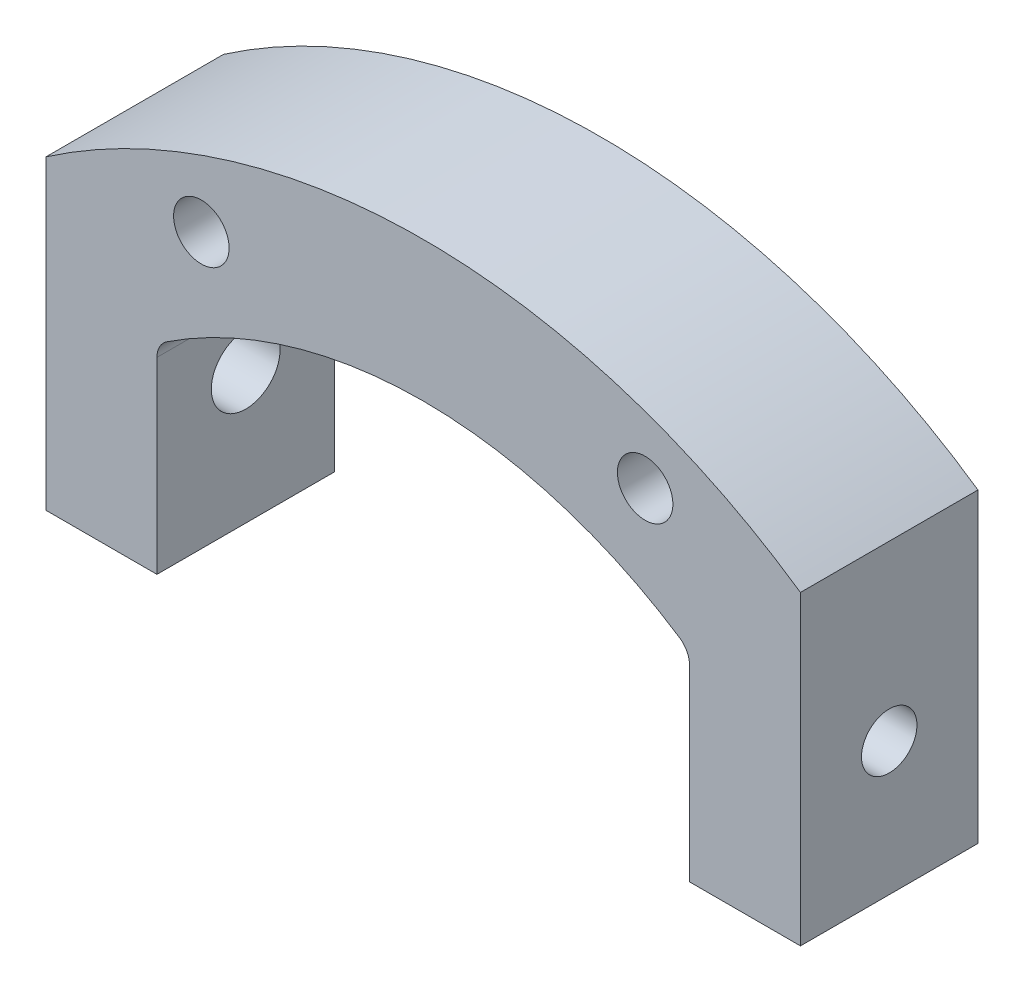
SolidWorks part; units mm, degrees
material "6061 合金"
ref_plane "前视基准面" through (0, 0, 0) normal (0, 0, 1) x (1, 0, 0)
ref_plane "上视基准面" through (0, 0, 0) normal (0, 1, 0) x (1, 0, 0)
ref_plane "右视基准面" through (0, 0, 0) normal (1, 0, 0) x (0, 0, -1)
sketch "草图4" plane through (0, 0, 0) normal (0, 0, 1) x (1, 0, 0)
  line L1 (-21.5, 5) -> (21.5, 5) construction
  line L2 (-21.5, 5) -> (-21.5, -5)
  line L3 (-21.5, -5) -> (21.5, -5)
  line L4 (21.5, 5) -> (21.5, -5)
  line L5 (0, -5) -> (0, 5) construction
  line L6 (-21.5, 0) -> (21.5, 0) construction
  arc A2 (-21.5, 5) -> (21.5, 5) centre (0, -15.9225) cw
  circle A3 centre (0, -18.9225) radius 30 construction
  circle A4 centre (-10, 9.3618) radius 1.25
  circle A5 centre (10, 9.3618) radius 1.25
  point P0 (0, 0)
  dimension "D3" = 20
  dimension "D6" = 30
  dimension "D7" = 60
  dimension "D9" = 2.5
  dimension "D1" = 43
  dimension "D2" = 10
  dimension "D8" = 3
extrude "凸台-拉伸2" add sketch "草图4" along normal blind 8
cosmetic thread "装饰螺纹线2" parameters "D2"=3
cosmetic thread "装饰螺纹线3" parameters "D2"=3
sketch "草图5" plane through (0, 0, 8) normal (0, 0, 1) x (1, 0, 0)
  line L0 (-21.5, -5) -> (21.5, -5) construction
  line L1 (-12, 4) -> (12, 4) construction
  line L2 (-12, 4) -> (-12, -5)
  line L3 (-12, -5) -> (12, -5)
  line L4 (12, 4) -> (12, -5)
  line L5 (0, -5) -> (0, 4) construction
  line L6 (-12, -0.5) -> (12, -0.5) construction
  line L7 (21.5, 13.1217) -> (17, 13.1217)
  line L8 (-21.5, -5) -> (-17, -5)
  line L9 (-21.5, -5) -> (-21.5, 13.1217)
  line L10 (-21.5, 13.1217) -> (-17, 13.1217)
  line L11 (-17, -5) -> (-17, 13.1217)
  line L12 (17, -5) -> (17, 13.1217)
  line L13 (21.5, -5) -> (17, -5)
  line L14 (21.5, -5) -> (21.5, 13.1217)
  arc A0 (-12, 4) -> (12, 4) centre (0, -13.2337) cw
  point P0 (0, -0.5)
  dimension "D3" = 21
  dimension "D1" = 9
  dimension "D2" = 24
  dimension "D4" = 5
extrude "切除-拉伸2" cut sketch "草图5" against normal through all
sketch "草图6" plane through (-17, 0, 0) normal (-1, 0, 0) x (0, 0, 1)
  line L0 (4, -5) -> (4, 8.7959) construction
  line L1 (0, -5) -> (8, -5) construction
  line L2 (0, 8.7959) -> (8, 8.7959) construction
  circle A0 centre (4, 1) radius 1.25
  dimension "D1" = 2.5
  dimension "D2" = 6
extrude "切除-拉伸3" cut sketch "草图6" against normal through all
cosmetic thread "装饰螺纹线1" parameters "D2"=3
sketch "草图7" plane through (-17, 0, 0) normal (-1, 0, 0) x (0, 0, 1)
  circle A0 centre (4, 1) radius 1.55
  dimension "D1" = 3.1
extrude "切除-拉伸4" cut sketch "草图7" against normal blind 6
fillet "圆角1" radius 1 2 edges at (12, 4, 4) (-12, 4, 4)
